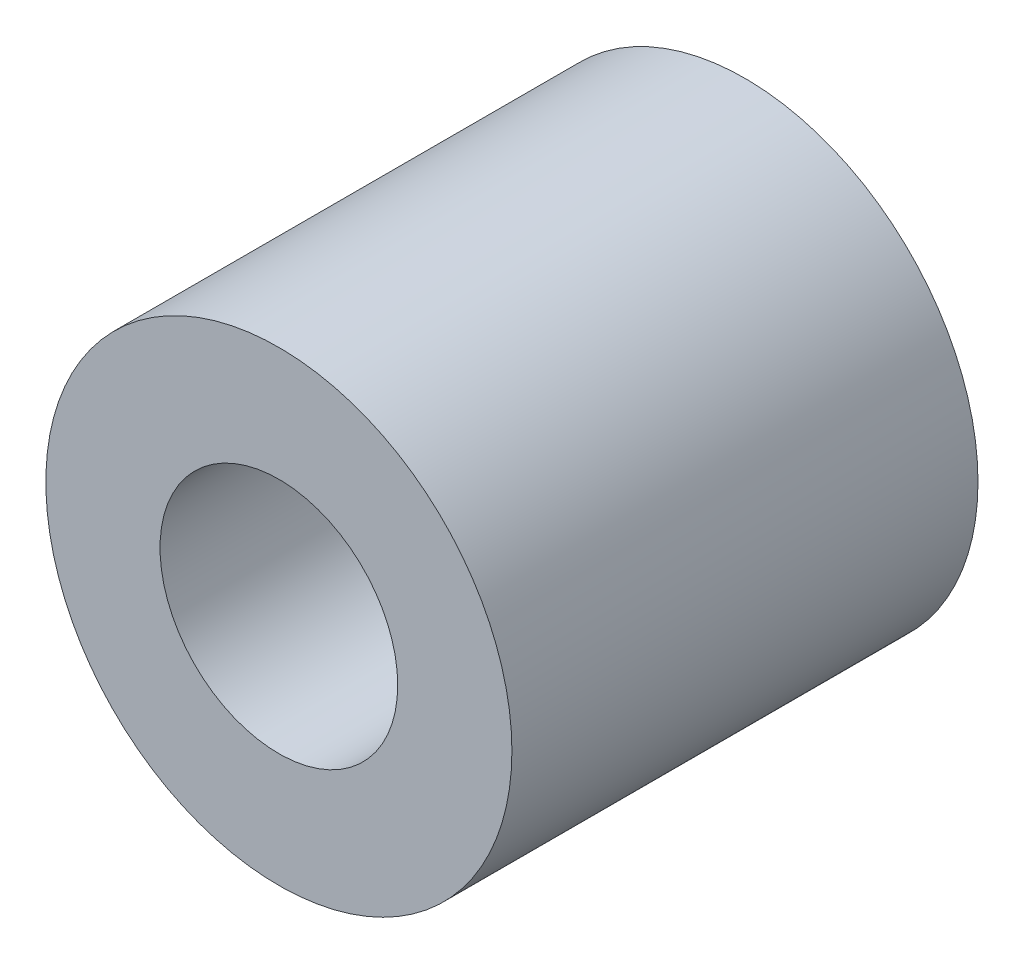
SolidWorks part; units mm, degrees
ref_plane "Front Plane" through (0, 0, 0) normal (0, 0, 1) x (1, 0, 0)
ref_plane "Top Plane" through (0, 0, 0) normal (0, 1, 0) x (1, 0, 0)
ref_plane "Right Plane" through (0, 0, 0) normal (1, 0, 0) x (0, 0, -1)
sketch "Sketch1" plane through (0, 0, 0) normal (0, 0, 1) x (1, 0, 0)
  line L0 (0, 6.477) -> (0, 12.7) construction
  line L1 (0, -6.477) -> (0, -12.7) construction
  circle A0 centre (0, 0) radius 12.7
  circle A1 centre (0, 0) radius 6.477
  dimension "OD" = 25.4
  dimension "ID" = 12.954
sketch "Sketch2" plane through (0, 0, 0) normal (1, 0, 0) x (0, 0, -1)
  line L0 (-12.7, 6.477) -> (12.7, 6.477) construction
  line L1 (-12.7, -6.477) -> (12.7, -6.477) construction
  line L2 (-12.7, -12.7) -> (12.7, -12.7) construction
  line L3 (-12.7, 12.7) -> (12.7, 12.7) construction
  dimension "Length" = 25.4
extrude "Extrude1" add sketch "Sketch1" along normal up to vertex (12.7 mm away) and the other way up to vertex (12.7 mm away) up to point (0, 6.477, 12.7) other way up to point (0, 6.477, -12.7)
sketch "Sketch3" plane through (0, 0, 12.7) normal (0, 0, 1) x (1, 0, 0)
  circle A0 centre (0, 0) radius 6.477 construction
  circle A3 centre (0, 0) radius 6.477
  point P3 (-6.477, 0)
